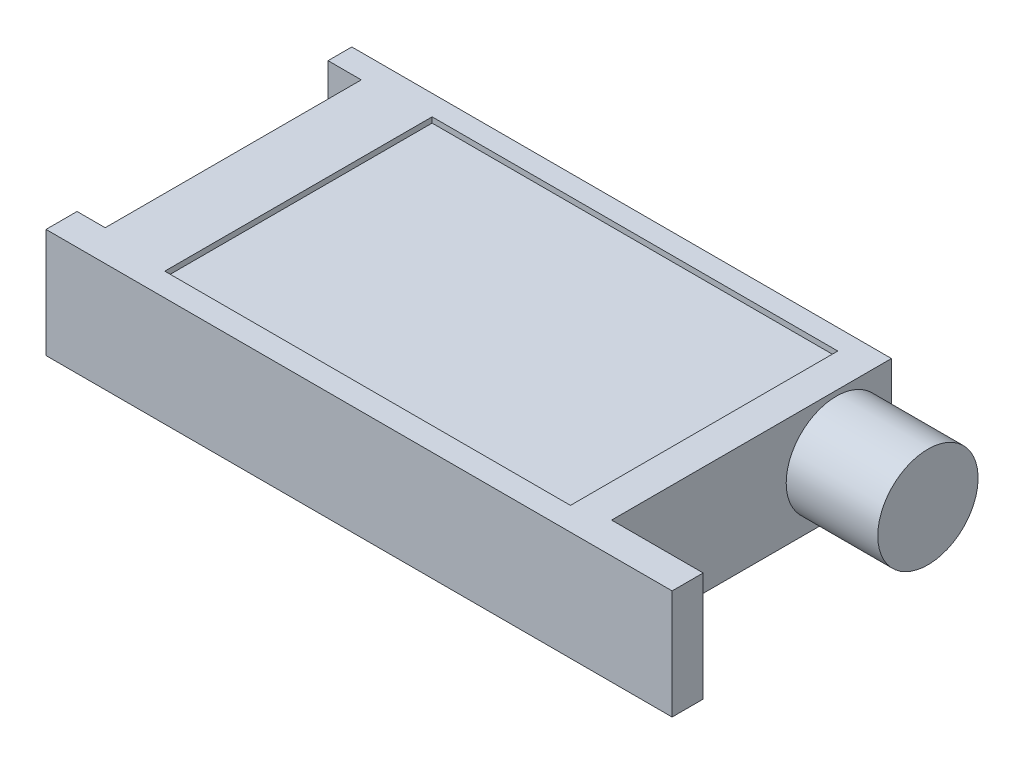
SolidWorks part; units mm, degrees
ref_plane "Front Plane" through (0, 0, 0) normal (0, 0, 1) x (1, 0, 0)
ref_plane "Top Plane" through (0, 0, 0) normal (0, 1, 0) x (1, 0, 0)
ref_plane "Right Plane" through (0, 0, 0) normal (1, 0, 0) x (0, 0, -1)
sketch "Sketch1" plane through (0, 0, 0) normal (0, 1, 0) x (1, 0, 0)
  line L0 (-50.0551, 21.6469) -> (-50.0551, -25.2262)
  line L1 (-31.6219, -30.9105) -> (17.9798, -30.9105)
  line L2 (-46.6564, 25.9992) -> (42.6293, 25.9992)
  line L3 (42.6293, 25.9992) -> (42.6293, -25.2262)
  line L4 (42.6293, -25.2262) -> (59.3918, -25.2262)
  line L5 (59.3918, -25.2262) -> (59.3918, -30.9105)
  line L6 (59.3918, -30.9105) -> (17.9798, -30.9105)
  line L7 (-31.6219, -30.9105) -> (-55.2066, -30.9105)
  line L8 (-55.2066, -30.9105) -> (-55.2066, -25.2262)
  line L9 (-55.2066, -25.2262) -> (-50.0551, -25.2262)
  line L10 (-46.6564, 25.9992) -> (-56.1422, 25.9992)
  line L11 (-56.1422, 25.9992) -> (-56.1422, 21.6469)
  line L12 (-56.1422, 21.6469) -> (-50.0551, 21.6469)
extrude "Boss-Extrude1" add sketch "Sketch1" along normal blind 20
sketch "Sketch2" plane through (42.6293, 0, 0) normal (1, 0, 0) x (0, 0, -1)
  circle A0 centre (15.9113, 9.8887) radius 9.1809
extrude "Boss-Extrude2" add sketch "Sketch2" along normal up to surface (16.7626 mm away) up to face at (59.3918, 10, 28.0684)
sketch "Sketch3" plane through (0, 20, 0) normal (0, 1, 0) x (1, 0, 0)
  line L1 (-37.7177, 22.2718) -> (36.5322, 22.2718)
  line L2 (-37.7177, 22.2718) -> (-37.7177, -26.6601)
  line L3 (-37.7177, -26.6601) -> (36.5322, -26.6601)
  line L4 (36.5322, 22.2718) -> (36.5322, -26.6601)
extrude "Cut-Extrude1" cut sketch "Sketch3" against normal blind 1
